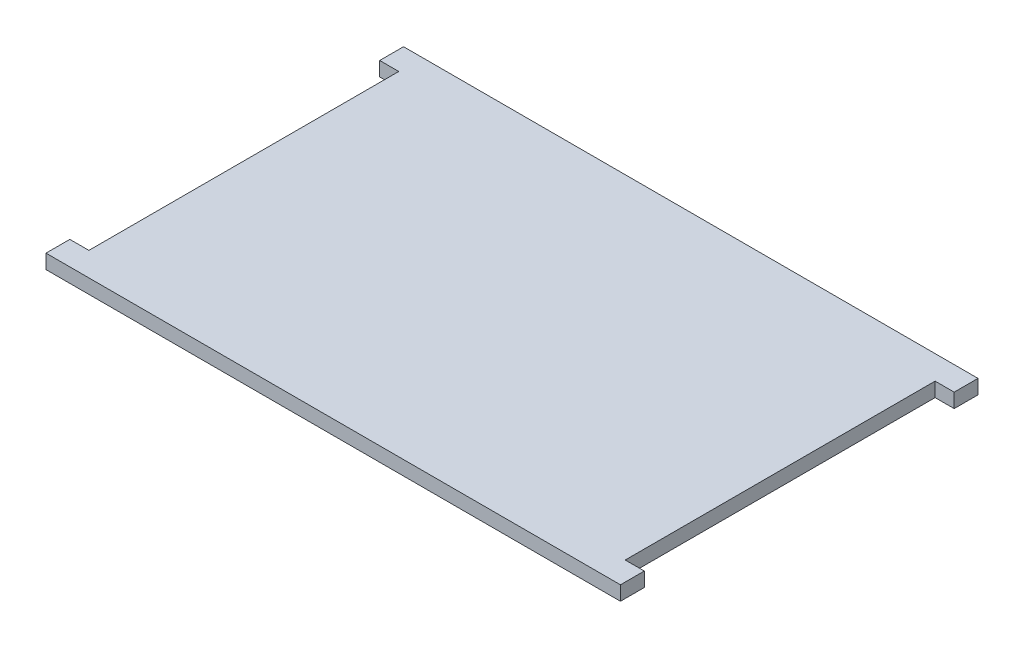
SolidWorks part; units mm, degrees
ref_plane "Front Plane" through (0, 0, 0) normal (0, 0, 1) x (1, 0, 0)
ref_plane "Top Plane" through (0, 0, 0) normal (0, 1, 0) x (1, 0, 0)
ref_plane "Right Plane" through (0, 0, 0) normal (1, 0, 0) x (0, 0, -1)
sketch "Sketch1" plane through (0, 0, 0) normal (0, 1, 0) x (1, 0, 0)
  line L1 (-120.5, 75) -> (120.5, 75)
  line L3 (-120.5, -75) -> (120.5, -75)
  line L7 (-120.5, 75) -> (-120.5, 65)
  line L8 (-120.5, 65) -> (-112.5, 65)
  line L9 (-112.5, 65) -> (-112.5, -65)
  line L10 (0, 132.496) -> (0, -180.1542) construction
  line L11 (-131.0103, 0) -> (171.5074, 0) construction
  line L13 (-120.5, -75) -> (-120.5, -65)
  line L14 (-120.5, -65) -> (-112.5, -65)
  line L15 (120.5, 65) -> (112.5, 65)
  line L16 (120.5, 75) -> (120.5, 65)
  line L19 (120.5, -75) -> (120.5, -65)
  line L20 (120.5, -65) -> (112.5, -65)
  line L23 (112.5, 65) -> (112.5, -65)
  point P0 (0, 0)
  dimension "D4" = 10
  dimension "D1" = 225
  dimension "D3" = 75
  dimension "D2" = 8
extrude "Boss-Extrude1" add sketch "Sketch1" along normal blind 6
sketch "Sketch3" plane through (120.5, 0, 0) normal (1, 0, 0) x (0, 0, -1)
  line L0 (-75, 6) -> (-65, 6) construction
  line L2 (65, 6) -> (75, 6) construction
  line L3 (65, 6) -> (65, 0) construction
  line L5 (-65, 6) -> (-65, 0) construction
  point P0 (-70, 3)
  point P3 (-70, 6)
  point P7 (70, 3)
  point P11 (70, 6)
  point P15 (65, 3)
  point P23 (-65, 3)
sketch "Sketch4" plane through (-120.5, 0, 0) normal (-1, 0, 0) x (0, 0, 1)
  line L0 (65, 6) -> (75, 6) construction
  line L1 (65, 6) -> (65, 0) construction
  line L2 (-75, 6) -> (-65, 6) construction
  line L3 (-65, 6) -> (-65, 0) construction
  point P0 (-70, 3)
  point P1 (70, 3)
  point P5 (70, 6)
  point P9 (65, 3)
  point P13 (-70, 6)
  point P17 (-65, 3)
equation "\"Material Thickness\"= 6mm"
equation "\"D1@Boss-Extrude1\"=\"Material Thickness\""
equation "\"D2@Sketch1\"=\"Material Thickness\"+2"
equation "\"D1@Sketch1\"=250-(\"Material Thickness\"*2)-13"
equation "\"D3@Sketch1\"=(160-10)/2"
